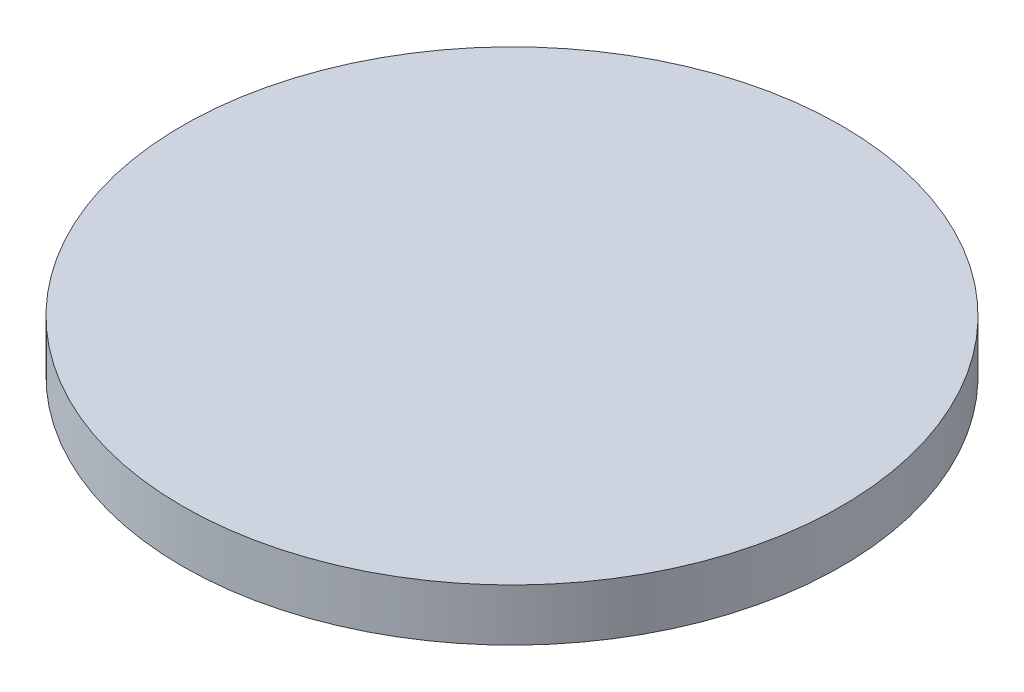
SolidWorks part; units mm, degrees
ref_plane "Front Plane" through (0, 0, 0) normal (0, 0, 1) x (1, 0, 0)
ref_plane "Top Plane" through (0, 0, 0) normal (0, 1, 0) x (1, 0, 0)
ref_plane "Right Plane" through (0, 0, 0) normal (1, 0, 0) x (0, 0, -1)
sketch "Sketch1" plane through (0, 0, 0) normal (0, 1, 0) x (1, 0, 0)
  circle A0 centre (0, 0) radius 13.915
  dimension "D1" = 27.83
extrude "Boss-Extrude1" add sketch "Sketch1" along normal blind 2.2
